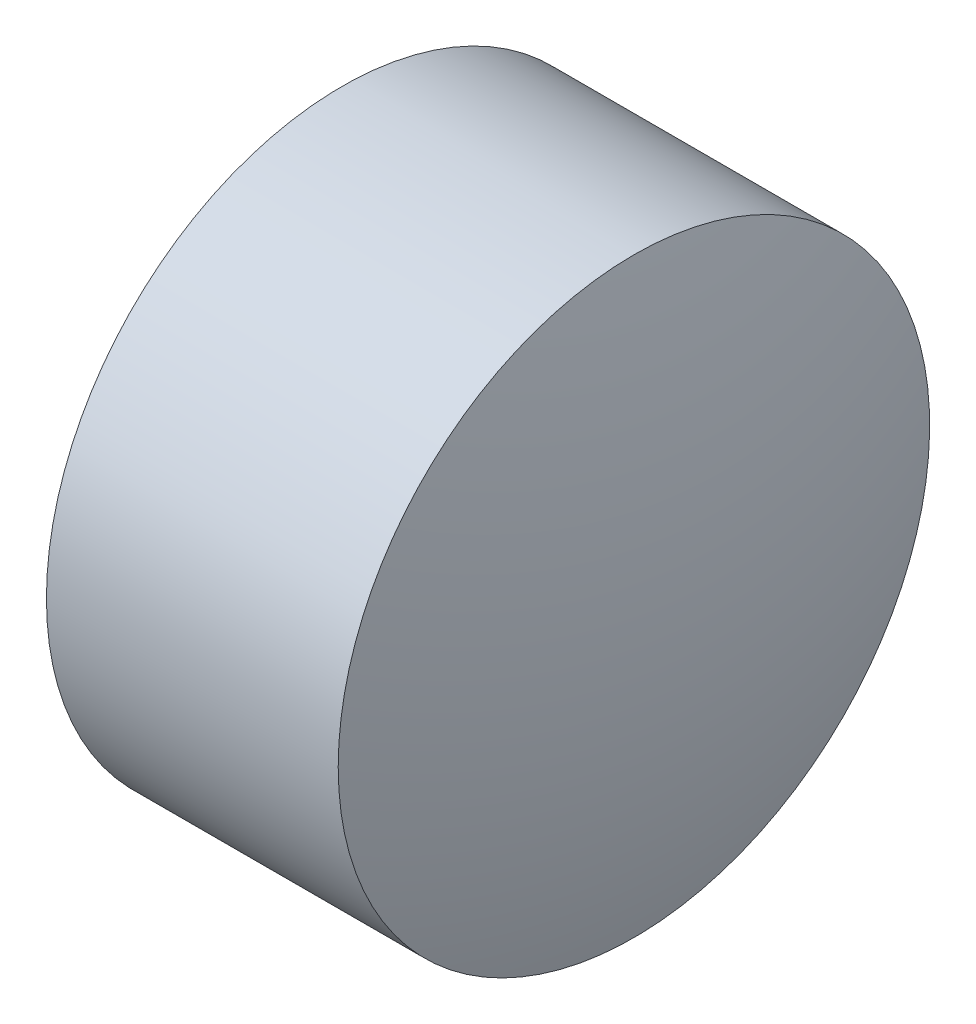
SolidWorks part; units mm, degrees
ref_plane "前视基准面" through (0, 0, 0) normal (0, 0, 1) x (1, 0, 0)
ref_plane "上视基准面" through (0, 0, 0) normal (0, 1, 0) x (1, 0, 0)
ref_plane "右视基准面" through (0, 0, 0) normal (1, 0, 0) x (0, 0, -1)
sketch "草图1" plane through (0, 0, 0) normal (0, 0, 1) x (1, 0, 0)
  line L0 (588.142, 193.8422) -> (586.662, 193.8422)
  line L1 (586.662, 193.8422) -> (586.662, 192.3422)
  line L2 (588.362, 192.3422) -> (586.662, 192.3422)
  line L3 (586.5226, 192.3422) -> (588.5051, 192.3422) construction
  arc A0 (588.362, 192.3422) -> (588.142, 193.8422) centre (583.1383, 192.3422) ccw
revolve "旋转1" add sketch "草图1" angle 360 about L3
